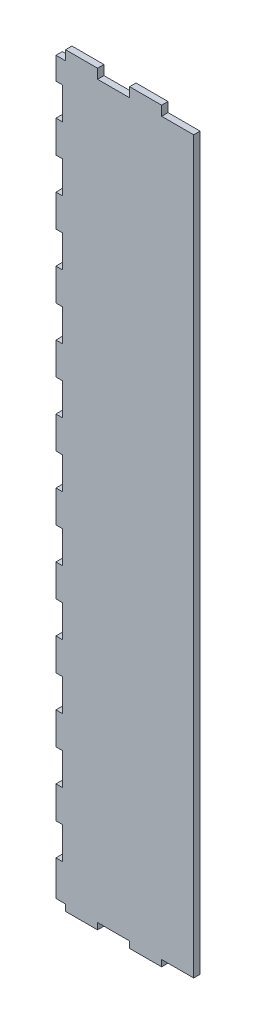
SolidWorks part; units mm, degrees
material "Verre"
ref_plane "Front Plane" through (0, 0, 0) normal (0, 0, 1) x (1, 0, 0)
ref_plane "Top Plane" through (0, 0, 0) normal (0, 1, 0) x (1, 0, 0)
ref_plane "Right Plane" through (0, 0, 0) normal (1, 0, 0) x (0, 0, -1)
sketch "Sketch1" plane through (0, 0, 0) normal (0, 0, 1) x (1, 0, 0)
  line L1 (0, 0) -> (40, 0)
  line L2 (0, 0) -> (0, 227)
  line L3 (0, 227) -> (40, 227)
  line L4 (40, 0) -> (40, 227)
  dimension "D1" = 40
  dimension "D2" = 227
extrude "Boss-Extrude1" add sketch "Sketch1" along normal blind 2
sketch "Sketch2" plane through (0, 0, 0) normal (0, -1, 0) x (1, 0, 0)
  line L0 (0, 0) -> (40, 0) construction
  line L1 (30, 0) -> (20, 0)
  line L2 (30, 0) -> (30, 2)
  line L3 (30, 2) -> (20, 2)
  line L4 (20, 0) -> (20, 2)
  line L5 (0, 2) -> (40, 2) construction
  line L6 (40, 2) -> (40, 0) construction
  dimension "D1" = 10
  dimension "D2" = 10
extrude "Boss-Extrude2" add sketch "Sketch2" along normal blind 3
pattern_linear "LPattern1" count 2 spacing 20 along (-1, 0, 0) of "Boss-Extrude2"
sketch "Sketch3" plane through (0, 227, 0) normal (0, 1, 0) x (1, 0, 0)
  line L0 (40, -2) -> (0, -2) construction
  line L1 (30, -2) -> (20, -2)
  line L2 (30, -2) -> (30, 0)
  line L3 (30, 0) -> (20, 0)
  line L4 (20, -2) -> (20, 0)
  line L5 (40, 0) -> (0, 0) construction
  line L6 (40, -2) -> (40, 0) construction
  point P10 (40, -1)
  dimension "D1" = 10
  dimension "D2" = 10
extrude "Boss-Extrude3" add sketch "Sketch3" along normal blind 3
pattern_linear "LPattern2" count 2 spacing 20 along (-1, 0, 0) of "Boss-Extrude3"
sketch "Sketch4" plane through (0, 0, 0) normal (-1, 0, 0) x (0, 0, 1)
  line L0 (2, 230) -> (2, -3) construction
  line L1 (0, 0) -> (2, 0)
  line L2 (0, 0) -> (0, 10)
  line L3 (0, 10) -> (2, 10)
  line L4 (2, 0) -> (2, 10)
  dimension "D1" = 10
extrude "Boss-Extrude4" add sketch "Sketch4" along normal blind 3
pattern_linear "LPattern3" count 12 spacing 20 along (0, 1, 0) of "Boss-Extrude4"
sketch "Esquisse1" plane through (0, 0, 2) normal (0, 0, 1) x (1, 0, 0)
  line L1 (-3, 230) -> (0, 230)
  line L2 (-3, 230) -> (-3, 227)
  line L3 (-3, 227) -> (0, 227)
  line L4 (0, 230) -> (0, 227)
  dimension "D1" = 3
  dimension "D2" = 3
extrude "Enlèv. mat.-Extru.1" cut sketch "Esquisse1" against normal through all
sketch "Esquisse2" plane through (0, 0, 2) normal (0, 0, 1) x (1, 0, 0)
  line L0 (-3, 0) -> (0, 0) construction
  line L1 (0, 227) -> (-1, 227)
  line L2 (0, 227) -> (0, 0)
  line L3 (0, 0) -> (-1, 0)
  line L4 (-1, 227) -> (-1, 0)
  line L10 (-3, 0) -> (40, 0)
  line L11 (-3, 0) -> (-3, -1)
  line L12 (-3, -1) -> (40, -1)
  line L13 (40, 0) -> (40, -1)
  dimension "D1" = 1
  dimension "D2" = 1
extrude "Boss.-Extru.1" add sketch "Esquisse2" against normal blind 2 contours L11 L12 L13 L10 | L3 L4 L1 L2
